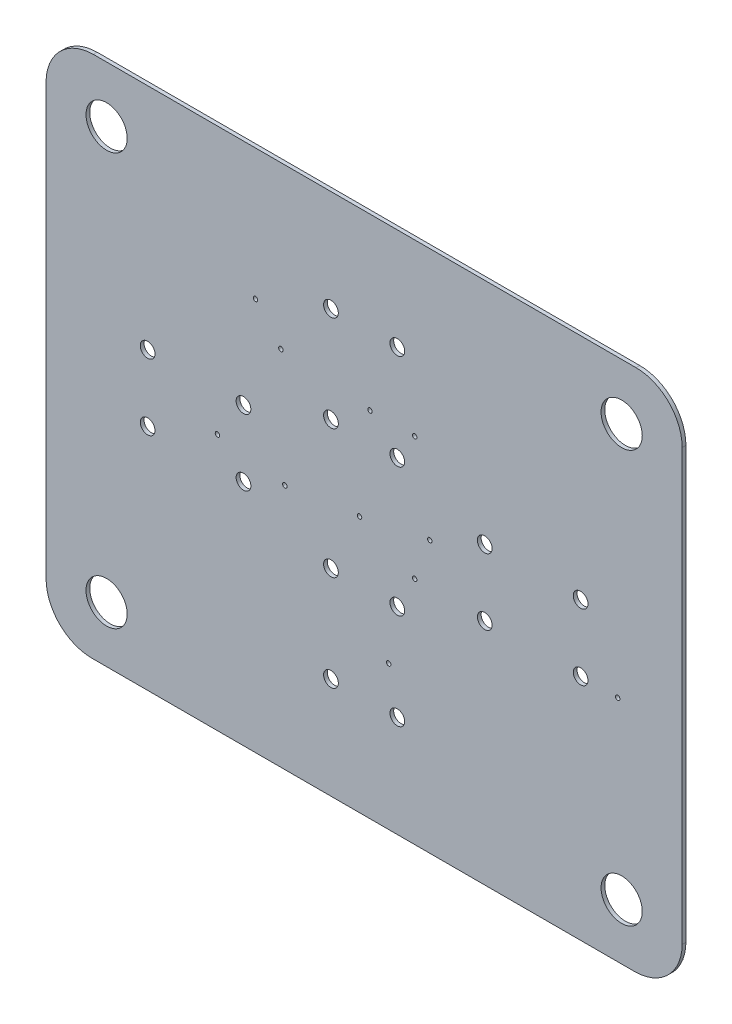
SolidWorks part; units mm, degrees
ref_plane "Front Plane" through (0, 0, 0) normal (0, 0, 1) x (1, 0, 0)
ref_plane "Top Plane" through (0, 0, 0) normal (0, 1, 0) x (1, 0, 0)
ref_plane "Right Plane" through (0, 0, 0) normal (1, 0, 0) x (0, 0, -1)
ref_plane "Conductive_Layer Bottom" through (0, 0, 0.034) normal (0, 0, 1) x (1, 0, 0)
ref_plane "Dielectric_Layer Bottom" through (0, 0, 0.288) normal (0, 0, 1) x (1, 0, 0)
ref_plane "Conductive_Layer Top" through (0, 0, 0.322) normal (0, 0, 1) x (1, 0, 0)
sketch "Sketch1" plane through (0, 0, 0) normal (0, 0, 1) x (1, 0, 0)
  line L0 (-21.565, 14.63) -> (-21.565, -14.63)
  line L1 (-18.44, -17.755) -> (18.364, -17.755)
  line L2 (21.565, -14.554) -> (21.565, 14.63)
  line L3 (18.44, 17.755) -> (-18.364, 17.755)
  arc A0 (-18.364, 17.755) -> (-21.565, 14.63) centre (-18.3208, 14.5089) ccw
  arc A1 (-21.565, -14.63) -> (-18.44, -17.755) centre (-18.459, -14.649) ccw
  arc A2 (18.364, -17.755) -> (21.565, -14.554) centre (18.3387, -14.5287) ccw
  arc A3 (21.565, 14.63) -> (18.44, 17.755) centre (18.4454, 14.6354) ccw
extrude "Board_Outline" add sketch "Sketch1" along normal blind 0.254 from offset 0.034 separate body
imported_body "Bottom"
imported_body "Top"
sketch "Sketch2" plane through (0, 0, 0) normal (0, 0, 1) x (1, 0, 0)
  circle A0 centre (-17.462, 13.97) radius 1.397
  circle A1 centre (17.462, -13.97) radius 1.397
  circle A2 centre (17.462, 13.97) radius 1.397
  circle A3 centre (-17.462, -13.97) radius 1.397
extrude "NPTH" cut sketch "Sketch2" along normal through all
sketch "Sketch3" plane through (0, 0, 0) normal (0, 0, 1) x (1, 0, 0)
  circle A0 centre (-2.25, 10.87) radius 0.5
  circle A1 centre (2.25, 10.87) radius 0.5
  circle A2 centre (2.25, 4.37) radius 0.5
  circle A3 centre (-2.25, 4.37) radius 0.5
  circle A4 centre (-8.18, 2.25) radius 0.5
  circle A5 centre (-8.18, -2.25) radius 0.5
  circle A6 centre (-14.68, -2.25) radius 0.5
  circle A7 centre (-14.68, 2.25) radius 0.5
  circle A8 centre (-2.25, -4.37) radius 0.5
  circle A9 centre (2.25, -4.37) radius 0.5
  circle A10 centre (2.25, -10.87) radius 0.5
  circle A11 centre (-2.25, -10.87) radius 0.5
  circle A12 centre (14.68, 2.25) radius 0.5
  circle A13 centre (14.68, -2.25) radius 0.5
  circle A14 centre (8.18, -2.25) radius 0.5
  circle A15 centre (8.18, 2.25) radius 0.5
  circle A16 centre (4.45, 0.635) radius 0.1525
  circle A17 centre (-7.366, 8.89) radius 0.1525
  circle A18 centre (3.43, -2.148) radius 0.1525
  circle A19 centre (3.43, 6.223) radius 0.1525
  circle A20 centre (-9.944, -0.354) radius 0.1525
  circle A21 centre (-0.313, -0.354) radius 0.1525
  circle A22 centre (0.398, 6.223) radius 0.1525
  circle A23 centre (-5.377, -1.065) radius 0.1525
  circle A24 centre (17.196, -2.25) radius 0.1525
  circle A25 centre (1.666, -8.001) radius 0.1525
  circle A26 centre (-5.645, 6.807) radius 0.1525
extrude "PTH" cut sketch "Sketch3" along normal through all
